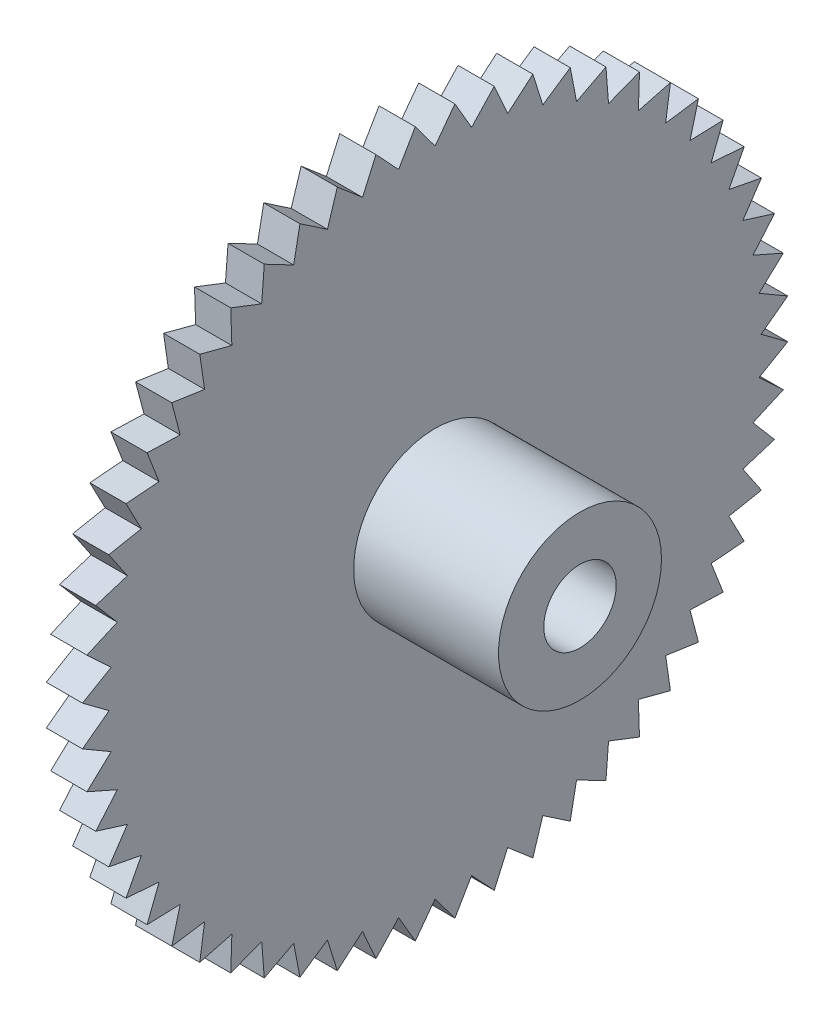
SolidWorks part; units mm, degrees
ref_plane "Front Plane" through (0, 0, 0) normal (0, 0, 1) x (1, 0, 0)
ref_plane "Top Plane" through (0, 0, 0) normal (0, 1, 0) x (1, 0, 0)
ref_plane "Right Plane" through (0, 0, 0) normal (1, 0, 0) x (0, 0, -1)
sketch "Sketch1" plane through (0, 0, 0) normal (1, 0, 0) x (0, 0, -1)
  circle A0 centre (0, 0) radius 19.5
extrude "Boss-Extrude1" add sketch "Sketch1" along normal blind 2
sketch "Sketch2" plane through (2, 0, 0) normal (1, 0, 0) x (0, 0, -1)
  circle A0 centre (0, 0) radius 4.5
extrude "Boss-Extrude2" add sketch "Sketch2" along normal blind 8
sketch "Sketch3" plane through (0, 0, 0) normal (-1, 0, 0) x (0, 0, 1)
  circle A0 centre (0, 0) radius 4.5
extrude "Boss-Extrude3" add sketch "Sketch3" along normal blind 1
sketch "Sketch4" plane through (10, 0, 0) normal (1, 0, 0) x (0, 0, -1)
  circle A0 centre (0, 0) radius 2
extrude "Cut-Extrude1" cut sketch "Sketch4" against normal blind 11
sketch "Sketch5" plane through (0, 0, 0) normal (-1, 0, 0) x (0, 0, 1)
  line L0 (0, 0) -> (0, 19.5)
  line L1 (0, 0) -> (-1.0934, 19.4693)
  line L2 (0, 0) -> (1.0934, 19.4693)
  line L3 (1.0934, 19.4693) -> (0, 18)
  line L4 (0, 18) -> (-1.0934, 19.4693)
  circle A0 centre (0, 0) radius 19.5 construction
  dimension "D1" = 1.5
extrude "Cut-Extrude5" cut sketch "Sketch5" against normal blind 2 contours L3 L0 | L4 L0
pattern_circular "CirPattern1" count 56 over 360 about axis through (0, 0, 0) along (1, 0, 0) of "Cut-Extrude5"
